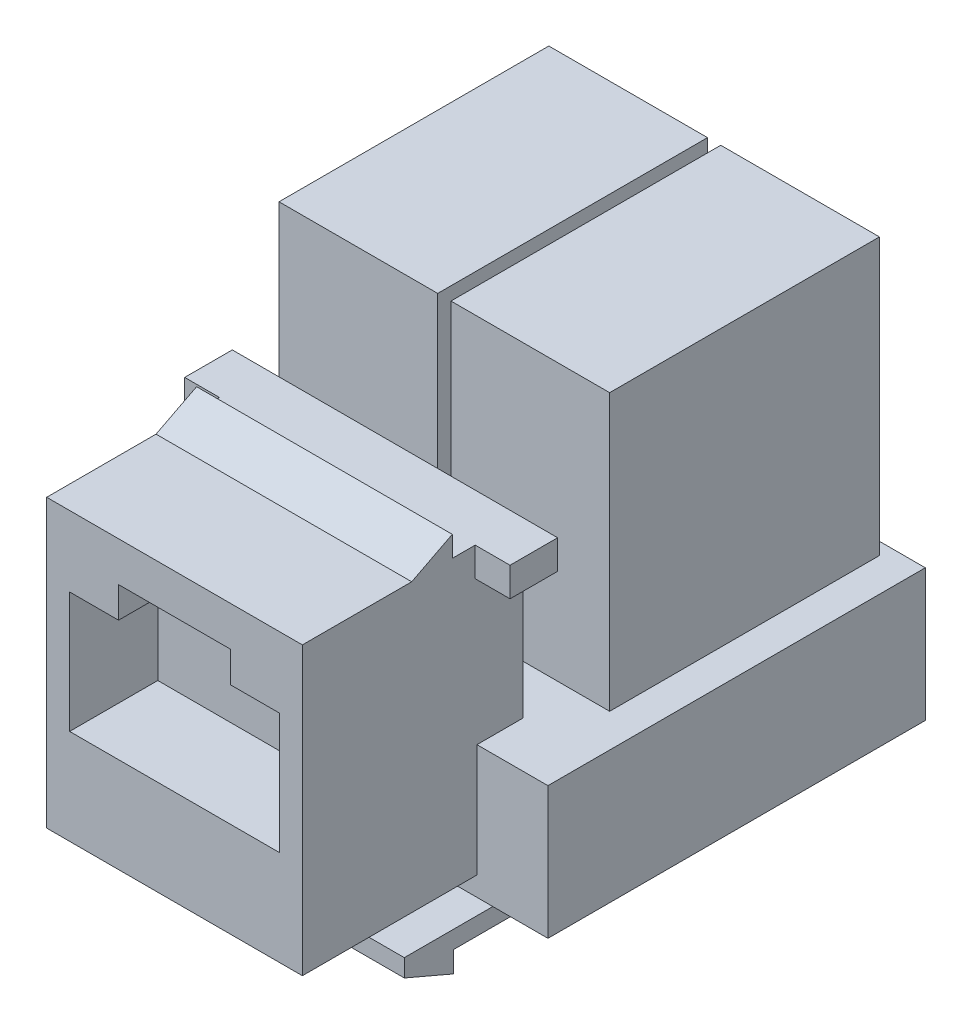
SolidWorks part; units mm, degrees
ref_plane "Plano frontal" through (0, 0, 0) normal (0, 0, 1) x (1, 0, 0)
ref_plane "Plano superior" through (0, 0, 0) normal (0, 1, 0) x (1, 0, 0)
ref_plane "Plano direito" through (0, 0, 0) normal (1, 0, 0) x (0, 0, -1)
sketch "Esboço1" plane through (0, 0, 0) normal (0, 0, 1) x (1, 0, 0)
  line L1 (-7.25, 8.125) -> (7.25, 8.125)
  line L2 (-7.25, 8.125) -> (-7.25, -8.125)
  line L3 (-7.25, -8.125) -> (7.25, -8.125)
  line L4 (7.25, 8.125) -> (7.25, -8.125)
  line L5 (-7.25, 8.125) -> (7.25, -8.125) construction
  line L6 (-7.25, -8.125) -> (7.25, 8.125) construction
  point P0 (0, 0)
  dimension "D1" = 14.5
  dimension "D2" = 16.25
extrude "Ressalto-extrusão1" add sketch "Esboço1" along normal blind 12.5
sketch "Esboço2" plane through (-7.25, 0, 0) normal (-1, 0, 0) x (0, 0, 1)
  line L0 (6.3, 8.125) -> (4, 9.305)
  line L1 (12.5, 8.125) -> (0, 8.125) construction
  line L2 (4, 9.305) -> (4, 8.125)
  line L3 (4, 8.125) -> (6.3, 8.125)
  line L4 (12.5, 8.125) -> (12.5, -8.125) construction
  dimension "D1" = 6.2
  dimension "D2" = 1.18
  dimension "D3" = 2.3
extrude "Ressalto-extrusão2" add sketch "Esboço2" against normal blind 14.5
sketch "Esboço3" plane through (0, 8.125, 0) normal (0, 1, 0) x (1, 0, 0)
  line L0 (7.25, 0) -> (-7.25, 0) construction
  line L1 (-9.225, 0) -> (9.225, 0)
  line L2 (-9.225, 0) -> (-9.225, -2.7)
  line L3 (-9.225, -2.7) -> (9.225, -2.7)
  line L4 (9.225, 0) -> (9.225, -2.7)
  point P6 (0, 0)
  dimension "D1" = 2.7
  dimension "D2" = 18.45
extrude "Ressalto-extrusão3" add sketch "Esboço3" against normal blind 1.65
sketch "Esboço4" plane through (0, 0, 12.5) normal (0, 0, 1) x (1, 0, 0)
  line L0 (-7.25, -8.125) -> (7.25, -8.125) construction
  line L1 (-5.95, 4.125) -> (-3.175, 4.125)
  line L2 (-5.95, 4.125) -> (-5.95, -2.725)
  line L3 (-5.95, -2.725) -> (5.95, -2.725)
  line L4 (5.95, 4.125) -> (5.95, -2.725)
  line L5 (3.175, 4.125) -> (5.95, 4.125)
  line L7 (-3.175, 4.125) -> (-3.175, 5.875)
  line L8 (-3.175, 5.875) -> (3.175, 5.875)
  line L9 (3.175, 4.125) -> (3.175, 5.875)
  point P4 (0, -2.725)
  point P12 (0, 5.875)
  dimension "D1" = 11.9
  dimension "D2" = 5.4
  dimension "D3" = 6.85
  dimension "D4" = 6.35
  dimension "D5" = 1.75
extrude "Corte-extrusão1" cut sketch "Esboço4" against normal blind 5
sketch "Esboço5" plane through (0, 0, 12.5) normal (0, 0, 1) x (1, 0, 0)
  line L0 (-9.225, 8.125) -> (-7.25, 8.125) construction
  line L1 (-11.275, -1.725) -> (11.275, -1.725)
  line L2 (-11.275, -1.725) -> (-11.275, -9.225)
  line L3 (-11.275, -9.225) -> (11.275, -9.225)
  line L4 (11.275, -1.725) -> (11.275, -9.225)
  point P4 (0, -9.225)
  dimension "D1" = 22.55
  dimension "D2" = 7.5
  dimension "D3" = 9.85
extrude "Ressalto-extrusão4" add sketch "Esboço5" against normal blind 21.4 from offset 9.9 offset against normal yes
sketch "Esboço6" plane through (0, -1.725, 0) normal (0, 1, 0) x (1, 0, 0)
  line L0 (-11.275, 18.8) -> (-11.275, -2.6) construction
  line L1 (-9.375, 18.1) -> (-0.375, 18.1)
  line L2 (-9.375, 18.1) -> (-9.375, 2.8)
  line L3 (-9.375, 2.8) -> (-0.375, 2.8)
  line L4 (-0.375, 18.1) -> (-0.375, 2.8)
  line L5 (0.375, 18.1) -> (9.375, 18.1)
  line L6 (0.375, 18.1) -> (0.375, 2.8)
  line L7 (0.375, 2.8) -> (9.375, 2.8)
  line L8 (9.375, 18.1) -> (9.375, 2.8)
  line L9 (11.275, 18.8) -> (11.275, -2.6) construction
  line L10 (11.275, 18.8) -> (-11.275, 18.8) construction
  dimension "D1" = 9
  dimension "D2" = 9
  dimension "D3" = 1.9
  dimension "D4" = 1.9
  dimension "D5" = 15.3
  dimension "D6" = 15.3
  dimension "D7" = 0.7
  dimension "D8" = 0.7
extrude "Ressalto-extrusão5" add sketch "Esboço6" along normal blind 15.65
sketch "Esboço7" plane through (-7.25, 0, 0) normal (-1, 0, 0) x (0, 0, 1)
  line L0 (-5.28, -9.225) -> (-5.28, -11.125)
  line L1 (-18.8, -9.225) -> (2.6, -9.225) construction
  line L2 (-5.28, -11.125) -> (6.72, -11.125)
  line L3 (6.72, -11.125) -> (6.72, -10.125)
  line L4 (6.72, -10.125) -> (-0.78, -10.125)
  line L5 (-0.78, -10.125) -> (-0.78, -9.225)
  line L6 (-0.78, -9.225) -> (-5.28, -9.225)
  line L7 (12.5, 8.125) -> (12.5, -8.125) construction
  point P10 (-3.1185, -9.225)
  dimension "D1" = 1
  dimension "D2" = 5.78
  dimension "D3" = 12
  dimension "D4" = 4.5
  dimension "D5" = 1.9
extrude "Ressalto-extrusão6" add sketch "Esboço7" against normal up to surface (14.5 mm away) up to face at (7.25, 3.1868, 4.5364)
sketch "Esboço8" plane through (-7.25, 0, 0) normal (-1, 0, 0) x (0, 0, 1)
  line L0 (6.72, -11.125) -> (3.92, -12.325)
  line L1 (3.92, -12.325) -> (3.92, -11.125)
  line L2 (-5.28, -11.125) -> (6.72, -11.125) construction
  line L3 (3.92, -11.125) -> (6.72, -11.125)
  dimension "D1" = 2.8
  dimension "D2" = 1.2
extrude "Ressalto-extrusão7" add sketch "Esboço8" against normal up to surface (14.5 mm away) up to face at (7.25, -10.1583, 0.22)
